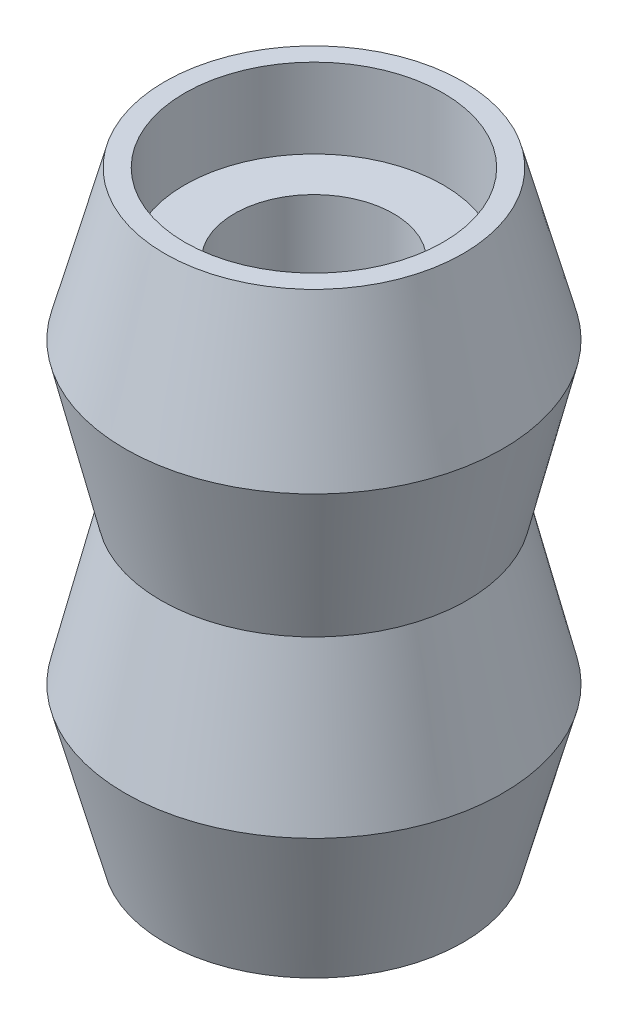
SolidWorks part; units mm, degrees
material "Maple"
ref_plane "Wasteboard" through (0, 0, 0) normal (0, 0, 1) x (1, 0, 0)
ref_plane "Left-Right" through (0, 0, 0) normal (0, 1, 0) x (1, 0, 0)
ref_plane "Front-Back" through (0, 0, 0) normal (1, 0, 0) x (0, 0, -1)
sketch "Sketch1" plane through (0, 0, 0) normal (0, 0, 1) x (1, 0, 0)
  line L0 (0, 42.3235) -> (0, -39.784) construction
  line L1 (0, -55) -> (0, 55) construction
  line L2 (0, 3.1923) -> (40.4814, 3.1923) construction
  line L3 (40.4814, 3.1923) -> (40.4814, 18.1923) construction
  line L4 (30.9163, 3.1923) -> (30.9163, 10.1923) construction
  line L5 (0, 30.7268) -> (2.5, 30.7268) construction
  line L6 (0, 37.5678) -> (4, 37.5678) construction
  line L7 (0, 43.5419) -> (6.5, 43.5419) construction
  line L8 (4, -7.8077) -> (4, 14.1923)
  line L9 (4, 14.1923) -> (6.5, 14.1923)
  line L10 (6.5, 14.1923) -> (6.5, 18.1923)
  line L11 (6.5, 18.1923) -> (7.5, 18.1923)
  line L12 (7.5, 18.1923) -> (9.5, 10.6923)
  line L13 (9.5, 10.6923) -> (7.7, 3.1923)
  line L14 (9.5, -4.3077) -> (7.7, 3.1923)
  line L15 (7.5, -11.8077) -> (9.5, -4.3077)
  line L16 (6.5, -11.8077) -> (7.5, -11.8077)
  line L17 (6.5, -7.8077) -> (6.5, -11.8077)
  line L18 (4, -7.8077) -> (6.5, -7.8077)
  point P25 (4, 3.1923)
  dimension "D1" = 15
  dimension "D2" = 7
  dimension "D3" = 4
  dimension "D4" = 2.5
  dimension "D5" = 6.5
  dimension "D6" = 2
  dimension "D7" = 7.5
  dimension "D8" = 15
  dimension "D9" = 6.5
  dimension "D10" = 82.1075
  dimension "D11" = 4
  dimension "D12" = 1
  dimension "D13" = 3.5
  dimension "D14" = 3.7
revolve "Revolve1" add sketch "Sketch1" angle 360 about L0
